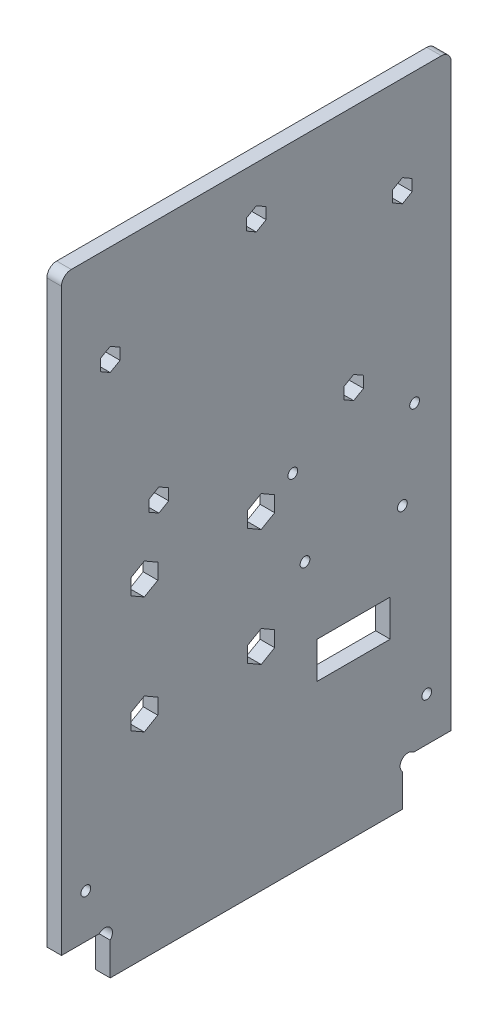
SolidWorks part; units mm, degrees
ref_plane "Plan de face" through (0, 0, 0) normal (0, 0, 1) x (1, 0, 0)
ref_plane "Plan de dessus" through (0, 0, 0) normal (0, 1, 0) x (1, 0, 0)
ref_plane "Plan de droite" through (0, 0, 0) normal (1, 0, 0) x (0, 0, -1)
sketch "Esquisse1" plane through (0, 0, 0) normal (1, 0, 0) x (0, 0, -1)
  line L8 (10, 6.7373) -> (10, 0)
  line L9 (70, 6.7373) -> (70, 0)
  line L10 (7.7373, 9) -> (0, 9)
  line L11 (10, 0) -> (70, 0)
  line L12 (72.2627, 9) -> (80, 9)
  line L13 (0, 9) -> (0, 130)
  line L14 (0, 130) -> (80, 130)
  line L15 (80, 130) -> (80, 9)
  arc A0 (10, 6.7373) -> (7.7373, 9) centre (8.8686, 7.8686) ccw
  arc A1 (70, 6.7373) -> (72.2627, 9) centre (71.1314, 7.8686) cw
  dimension "D7" = 1.1314
  dimension "D6" = 1.6
  dimension "D1" = 9
  dimension "D2" = 10
  dimension "D3" = 10
  dimension "D4" = 80
  dimension "D5" = 130
  dimension "D8" = 1.1314
  dimension "D9" = 1.1314
  dimension "D10" = 1.1314
extrude "Extrusion1" add sketch "Esquisse1" along normal blind 3
sketch "Esquisse2" plane through (3, 0, 0) normal (1, 0, 0) x (0, 0, -1)
  line L0 (0, 9) -> (7.7373, 9) construction
  line L1 (0, 130) -> (0, 9) construction
  line L2 (80, 9) -> (80, 130) construction
  line L3 (72.2627, 9) -> (80, 9) construction
  line L4 (80, 130) -> (0, 130) construction
  circle A0 centre (60, 80) radius 1
  circle A1 centre (10, 110) radius 1
  circle A2 centre (20, 80) radius 1
  circle A3 centre (70, 110) radius 1
  circle A4 centre (17, 67.45) radius 1.5
  circle A5 centre (17, 43.45) radius 1.5
  circle A6 centre (41, 43.45) radius 1.5
  circle A7 centre (41, 67.45) radius 1.5
  circle A8 centre (40, 120) radius 1
  circle A9 centre (70, 54) radius 1
  circle A10 centre (50, 54) radius 1
  dimension "D5" = 17
  dimension "D7" = 10
  dimension "D9" = 10
  dimension "D4" = 3
  dimension "D6" = 2
  dimension "D1" = 58.45
  dimension "D2" = 24
  dimension "D3" = 24
  dimension "D8" = 40
  dimension "D10" = 30
  dimension "D11" = 10
  dimension "D12" = 20
  dimension "D13" = 10
  dimension "D14" = 10
  dimension "D15" = 10
  dimension "D16" = 20
  dimension "D17" = 45
extrude "Enlèv. mat.-Extru.1" cut sketch "Esquisse2" against normal through all
sketch "Esquisse3" plane through (0, 0, 0) normal (-1, 0, 0) x (0, 0, 1)
  line L1 (-67.5, 39) -> (-52.5, 39)
  line L2 (-67.5, 39) -> (-67.5, 31.5)
  line L3 (-67.5, 31.5) -> (-52.5, 31.5)
  line L4 (-52.5, 39) -> (-52.5, 31.5)
  circle A0 centre (-70, 54) radius 1 construction
  circle A1 centre (-50, 54) radius 1 construction
  dimension "D4" = 2.5
  dimension "D1" = 15
  dimension "D2" = 7.5
  dimension "D3" = 15
  dimension "D5" = 2.5
extrude "Enlèv. mat.-Extru.2" cut sketch "Esquisse3" against normal through all
sketch "Esquisse4" plane through (3, 0, 0) normal (1, 0, 0) x (0, 0, -1)
  line L3 (0, 9) -> (7.7373, 9) construction
  line L4 (0, 130) -> (0, 9) construction
  line L5 (80, 9) -> (80, 130) construction
  circle A2 centre (75, 18) radius 1
  circle A3 centre (5, 18) radius 1
  dimension "D1" = 2
  dimension "D2" = 5
  dimension "D3" = 5
  dimension "D5" = 9
extrude "Enlèv. mat.-Extru.3" cut sketch "Esquisse4" against normal through all
sketch "Esquisse5" plane through (3, 0, 0) normal (1, 0, 0) x (0, 0, -1)
  line L0 (0, 130) -> (0, 9) construction
  line L1 (12.0178, 111.165) -> (10, 112.33)
  line L2 (10, 112.33) -> (7.9822, 111.165)
  line L3 (7.9822, 111.165) -> (7.9822, 108.835)
  line L4 (7.9822, 108.835) -> (10, 107.67)
  line L5 (10, 107.67) -> (12.0178, 108.835)
  line L6 (12.0178, 108.835) -> (12.0178, 111.165)
  line L7 (0, 130) -> (0, 9) construction
  line L26 (42.0178, 118.835) -> (42.0178, 121.165)
  line L27 (42.0178, 121.165) -> (40, 122.33)
  line L28 (40, 122.33) -> (37.9822, 121.165)
  line L29 (37.9822, 121.165) -> (37.9822, 118.835)
  line L30 (37.9822, 118.835) -> (40, 117.67)
  line L31 (40, 117.67) -> (42.0178, 118.835)
  line L32 (70, 107.67) -> (72.0178, 108.835)
  line L33 (72.0178, 108.835) -> (72.0178, 111.165)
  line L34 (72.0178, 111.165) -> (70, 112.33)
  line L35 (70, 112.33) -> (67.9822, 111.165)
  line L36 (67.9822, 111.165) -> (67.9822, 108.835)
  line L37 (67.9822, 108.835) -> (70, 107.67)
  line L38 (62.0178, 78.835) -> (62.0178, 81.165)
  line L39 (62.0178, 81.165) -> (60, 82.33)
  line L40 (60, 82.33) -> (57.9822, 81.165)
  line L41 (57.9822, 81.165) -> (57.9822, 78.835)
  line L42 (57.9822, 78.835) -> (60, 77.67)
  line L43 (60, 77.67) -> (62.0178, 78.835)
  line L44 (22.0178, 78.835) -> (22.0178, 81.165)
  line L45 (22.0178, 81.165) -> (20, 82.33)
  line L46 (20, 82.33) -> (17.9822, 81.165)
  line L47 (17.9822, 81.165) -> (17.9822, 78.835)
  line L48 (17.9822, 78.835) -> (20, 77.67)
  line L49 (20, 77.67) -> (22.0178, 78.835)
  line L56 (43.7713, 65.85) -> (43.7713, 69.05)
  line L57 (43.7713, 69.05) -> (41, 70.65)
  line L58 (41, 70.65) -> (38.2287, 69.05)
  line L59 (38.2287, 69.05) -> (38.2287, 65.85)
  line L60 (38.2287, 65.85) -> (41, 64.25)
  line L61 (41, 64.25) -> (43.7713, 65.85)
  line L62 (43.7713, 41.85) -> (43.7713, 45.05)
  line L63 (43.7713, 45.05) -> (41, 46.65)
  line L64 (41, 46.65) -> (38.2287, 45.05)
  line L65 (38.2287, 45.05) -> (38.2287, 41.85)
  line L66 (38.2287, 41.85) -> (41, 40.25)
  line L67 (41, 40.25) -> (43.7713, 41.85)
  line L68 (19.7713, 41.85) -> (19.7713, 45.05)
  line L69 (19.7713, 45.05) -> (17, 46.65)
  line L70 (17, 46.65) -> (14.2287, 45.05)
  line L71 (14.2287, 45.05) -> (14.2287, 41.85)
  line L72 (14.2287, 41.85) -> (17, 40.25)
  line L73 (17, 40.25) -> (19.7713, 41.85)
  line L75 (19.7713, 65.85) -> (19.7713, 69.05)
  line L76 (19.7713, 69.05) -> (17, 70.65)
  line L77 (17, 70.65) -> (14.2287, 69.05)
  line L78 (14.2287, 69.05) -> (14.2287, 65.85)
  line L79 (14.2287, 65.85) -> (17, 64.25)
  line L80 (17, 64.25) -> (19.7713, 65.85)
  circle A0 centre (10, 110) radius 2.0178 construction
  circle A1 centre (40, 120) radius 2.0178 construction
  circle A2 centre (70, 110) radius 2.0178 construction
  circle A3 centre (60, 80) radius 2.0178 construction
  circle A4 centre (20, 80) radius 2.0178 construction
  circle A5 centre (17, 67.45) radius 2.7713 construction
  circle A6 centre (41, 67.45) radius 2.7713 construction
  circle A7 centre (41, 43.45) radius 2.7713 construction
  circle A8 centre (17, 43.45) radius 2.7713 construction
  dimension "D1" = 2.33
  dimension "D2" = 2.33
  dimension "D3" = 2.33
  dimension "D4" = 2.33
  dimension "D5" = 2.33
  dimension "D6" = 3.2
  dimension "D7" = 3.2
  dimension "D8" = 3.2
  dimension "D9" = 3.2
extrude "Enlèv. mat.-Extru.4" cut sketch "Esquisse5" against normal through all
fillet "Congé1" radius 2 2 edges at (1.5, 130, -80) (1.5, 130, 0)
sketch "Esquisse6" plane through (0, 0, 0) normal (-1, 0, 0) x (0, 0, 1)
  line L1 (-67.5, 39) -> (-67.5, 31.5) construction
  line L2 (-52.5, 31.5) -> (-52.5, 39) construction
  circle A0 centre (-72.5, 71) radius 1
  circle A1 centre (-47.5, 71) radius 1
  circle A2 centre (-70, 54) radius 1 construction
  dimension "D1" = 2
  dimension "D2" = 2
  dimension "D3" = 17
  dimension "D4" = 5
  dimension "D5" = 5
extrude "Enlèv. mat.-Extru.5" cut sketch "Esquisse6" against normal through all
